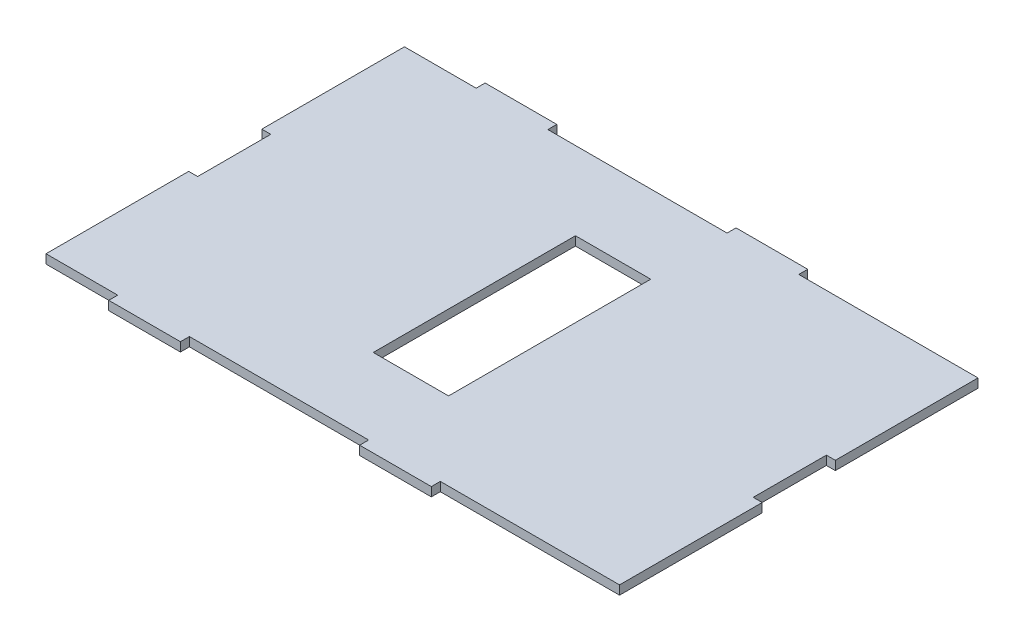
SolidWorks part; units mm, degrees
ref_plane "Front Plane" through (0, 0, 0) normal (0, 0, 1) x (1, 0, 0)
ref_plane "Top Plane" through (0, 0, 0) normal (0, 1, 0) x (1, 0, 0)
ref_plane "Right Plane" through (0, 0, 0) normal (1, 0, 0) x (0, 0, -1)
sketch "Sketch1" plane through (0, 0, 0) normal (0, 1, 0) x (1, 0, 0)
  line L1 (-7.5108, 38.9535) -> (195.6892, 38.9535)
  line L2 (-7.5108, 38.9535) -> (-7.5108, -88.0465)
  line L3 (-7.5108, -88.0465) -> (195.6892, -88.0465)
  line L4 (195.6892, 38.9535) -> (195.6892, -88.0465)
  dimension "D1" = 203.2
  dimension "D2" = 127
extrude "Boss-Extrude1" add sketch "Sketch1" along normal blind 3.175
sketch "Sketch2" plane through (0, 0, 88.0465) normal (0, 0, 1) x (1, 0, 0)
  line L0 (-7.5108, 3.175) -> (195.6892, 3.175) construction
  line L1 (106.7892, 3.175) -> (132.1892, 3.175)
  line L2 (106.7892, 3.175) -> (106.7892, 0)
  line L3 (106.7892, 0) -> (132.1892, 0)
  line L4 (132.1892, 3.175) -> (132.1892, 0)
  line L5 (-7.5108, 0) -> (195.6892, 0) construction
  line L6 (195.6892, 3.175) -> (195.6892, 0) construction
  line L7 (17.8892, 3.175) -> (43.2892, 3.175)
  line L8 (17.8892, 3.175) -> (17.8892, 0)
  line L9 (17.8892, 0) -> (43.2892, 0)
  line L10 (43.2892, 3.175) -> (43.2892, 0)
  dimension "D1" = 25.4
  dimension "D2" = 25.4
  dimension "D3" = 63.5
  dimension "D4" = 63.5
extrude "Boss-Extrude2" add sketch "Sketch2" along normal blind 3.175
sketch "Sketch3" plane through (0, 0, -38.9535) normal (0, 0, -1) x (-1, 0, 0)
  line L0 (-195.6892, 3.175) -> (7.5108, 3.175) construction
  line L1 (-132.1892, 3.175) -> (-106.7892, 3.175)
  line L2 (-132.1892, 3.175) -> (-132.1892, 0)
  line L3 (-132.1892, 0) -> (-106.7892, 0)
  line L4 (-106.7892, 3.175) -> (-106.7892, 0)
  line L5 (-195.6892, 0) -> (7.5108, 0) construction
  line L7 (-43.2892, 3.175) -> (-17.8892, 3.175)
  line L8 (-43.2892, 3.175) -> (-43.2892, 0)
  line L9 (-43.2892, 0) -> (-17.8892, 0)
  line L10 (-17.8892, 3.175) -> (-17.8892, 0)
  point P12 (0, 0)
  point P13 (0, 0)
  dimension "D1" = 25.4
  dimension "D2" = 25.4
extrude "Boss-Extrude3" add sketch "Sketch3" along normal blind 3.175
sketch "Sketch4" plane through (195.6892, 0, 0) normal (1, 0, 0) x (0, 0, -1)
  line L0 (-88.0465, 3.175) -> (38.9535, 3.175) construction
  line L1 (-37.5005, 3.175) -> (-11.5925, 3.175)
  line L2 (-37.5005, 3.175) -> (-37.5005, 0)
  line L3 (-37.5005, 0) -> (-11.5925, 0)
  line L4 (-11.5925, 3.175) -> (-11.5925, 0)
  line L5 (-88.0465, 0) -> (38.9535, 0) construction
  line L6 (-88.0465, 3.175) -> (-88.0465, 0) construction
  dimension "D1" = 25.908
  dimension "D2" = 50.546
extrude "Cut-Extrude1" cut sketch "Sketch4" against normal blind 3.175
sketch "Sketch5" plane through (-7.5108, 0, 0) normal (-1, 0, 0) x (0, 0, 1)
  line L0 (-38.9535, 3.175) -> (88.0465, 3.175) construction
  line L1 (37.5005, 3.175) -> (11.5925, 3.175)
  line L2 (37.5005, 3.175) -> (37.5005, 0)
  line L3 (37.5005, 0) -> (11.5925, 0)
  line L4 (11.5925, 3.175) -> (11.5925, 0)
  line L5 (-38.9535, 0) -> (88.0465, 0) construction
  point P8 (0, 0)
  dimension "D1" = 25.908
extrude "Cut-Extrude2" cut sketch "Sketch5" against normal blind 3.175
sketch "Sketch7" plane through (0, 3.175, 0) normal (0, 1, 0) x (1, 0, 0)
  line L0 (94.0892, -88.0465) -> (94.0892, 38.9535) construction
  line L1 (43.2892, -88.0465) -> (106.7892, -88.0465) construction
  line L2 (106.7892, 38.9535) -> (43.2892, 38.9535) construction
  line L3 (192.5142, -24.5465) -> (-4.3358, -24.5465) construction
  line L4 (192.5142, -11.5925) -> (192.5142, -37.5005) construction
  line L5 (-4.3358, -37.5005) -> (-4.3358, -11.5925) construction
  line L7 (195.6892, -11.5925) -> (195.6892, 38.9535) construction
  line L8 (195.6892, 38.9535) -> (132.1892, 38.9535) construction
  line L10 (107.4242, -60.3605) -> (80.7542, -60.3605)
  line L11 (107.4242, -60.3605) -> (107.4242, 11.2675)
  line L12 (107.4242, 11.2675) -> (80.7542, 11.2675)
  line L13 (80.7542, -60.3605) -> (80.7542, 11.2675)
  line L14 (107.4242, -60.3605) -> (80.7542, 11.2675) construction
  line L15 (107.4242, 11.2675) -> (80.7542, -60.3605) construction
  point P16 (94.0892, -24.5465)
  dimension "D1" = 101.6
  dimension "D2" = 63.5
  dimension "D3" = 71.628
  dimension "D4" = 26.67
extrude "Cut-Extrude3" cut sketch "Sketch7" against normal blind 3.175
